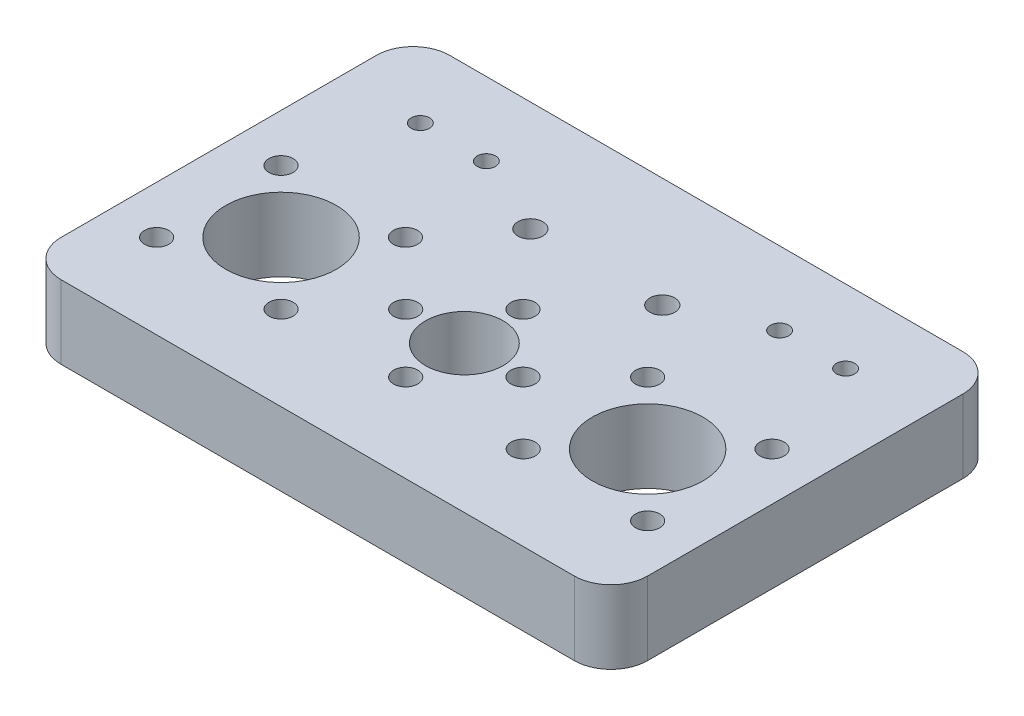
SolidWorks part; units mm, degrees
ref_plane "前视基准面" through (0, 0, 0) normal (0, 0, 1) x (1, 0, 0)
ref_plane "上视基准面" through (0, 0, 0) normal (0, 1, 0) x (1, 0, 0)
ref_plane "右视基准面" through (0, 0, 0) normal (1, 0, 0) x (0, 0, -1)
sketch "草图1" plane through (0, 0, 0) normal (0, 1, 0) x (1, 0, 0)
  line L0 (-107.5099, 0) -> (110.7056, 0) construction
  line L1 (0, 60.3977) -> (0, -44.8569) construction
  line L2 (-25, 60.3977) -> (-25, -44.8569) construction
  line L3 (25, 60.3977) -> (25, -44.8569) construction
  line L4 (-25, 0) -> (-39.1277, 14.1277) construction
  line L5 (-25, 82.5099) -> (-25, -135.7056) construction
  line L6 (57.5099, 0) -> (-160.7056, 0) construction
  line L7 (-25, -82.5099) -> (-25, 135.7056) construction
  line L8 (-107.5099, 23) -> (110.7056, 23) construction
  line L9 (-20, 60.3977) -> (-20, -44.8569) construction
  line L10 (20, 60.3977) -> (20, -44.8569) construction
  line L11 (-35, 33) -> (35, 33)
  line L12 (-40, 28) -> (-40, -15)
  line L13 (40, 28) -> (40, -15)
  line L14 (-35, -20) -> (35, -20)
  line L15 (-40, 60.3977) -> (-40, -44.8569) construction
  line L16 (-107.5099, -20) -> (110.7056, -20) construction
  line L17 (40, 60.3977) -> (40, -44.8569) construction
  line L18 (-107.5099, 33) -> (110.7056, 33) construction
  circle A0 centre (0, 0) radius 5.3
  circle A1 centre (0, 0) radius 8 construction
  circle A2 centre (0, 8) radius 1.65
  circle A3 centre (8, 0) radius 1.65
  circle A4 centre (0, -8) radius 1.65
  circle A5 centre (-8, 0) radius 1.65
  circle A6 centre (-25, 0) radius 7.55
  circle A7 centre (-25, 0) radius 12 construction
  circle A8 centre (-33.4853, 8.4853) radius 1.65
  circle A9 centre (-16.5147, 8.4853) radius 1.65
  circle A10 centre (-16.5147, -8.4853) radius 1.65
  circle A11 centre (-33.4853, -8.4853) radius 1.65
  circle A12 centre (-16.5147, 8.4853) radius 1.65
  circle A13 centre (-33.4853, -8.4853) radius 1.65
  circle A14 centre (25, 0) radius 7.55
  circle A15 centre (16.5147, 8.4853) radius 1.65
  circle A16 centre (16.5147, -8.4853) radius 1.65
  circle A17 centre (33.4853, -8.4853) radius 1.65
  circle A18 centre (33.4853, 8.4853) radius 1.65
  circle A19 centre (-20, 23) radius 1.25
  circle A20 centre (0, 23) radius 1.25 construction
  circle A21 centre (20, 23) radius 1.25
  arc A22 (-40, -15) -> (-35, -20) centre (-35, -15) ccw
  arc A23 (35, -20) -> (40, -15) centre (35, -15) ccw
  arc A24 (40, 28) -> (35, 33) centre (35, 28) ccw
  arc A25 (-35, 33) -> (-40, 28) centre (-35, 28) ccw
  circle A26 centre (-29, 23) radius 1.25
  circle A27 centre (29, 23) radius 1.25
  dimension "D1" = 3.3
  dimension "D2" = 10.6
  dimension "D3" = 16
  dimension "D7" = 24
  dimension "D8" = 15.1
  dimension "D10" = 3.3
  dimension "D15" = 2.5
  dimension "D21" = 5
  dimension "D22" = 2.5
  dimension "D9" = 45
  dimension "D23" = 9
  dimension "D5" = 25
  dimension "D6" = 25
  dimension "D12" = 23
  dimension "D13" = 20
  dimension "D14" = 20
  dimension "D17" = 10
  dimension "D18" = 40
  dimension "D19" = 40
  dimension "D20" = 53
  dimension "D16" = 3
  dimension "D4" = 4
  dimension "D11" = 4
extrude "凸台-拉伸1" add sketch "草图1" along normal blind 10 contours L11 A25 L12 A22 L14 A23 L13 A24 A18 A16 A14 A11 A10 A9 A8 A6 A5 A4 A3 A2 A0 A15 A17 A19 A20 A21
sketch "草图2" plane through (0, 10, 0) normal (0, 1, 0) x (1, 0, 0)
  line L0 (0, 33) -> (0, -20) construction
  line L1 (-35, 33) -> (35, 33) construction
  line L2 (-35, -20) -> (35, -20) construction
  circle A0 centre (-9, 18) radius 1.7
  circle A1 centre (9, 18) radius 1.7
  dimension "D1" = 3.4
  dimension "D2" = 18
  dimension "D3" = 18
extrude "切除-拉伸1" cut sketch "草图2" against normal blind 10
